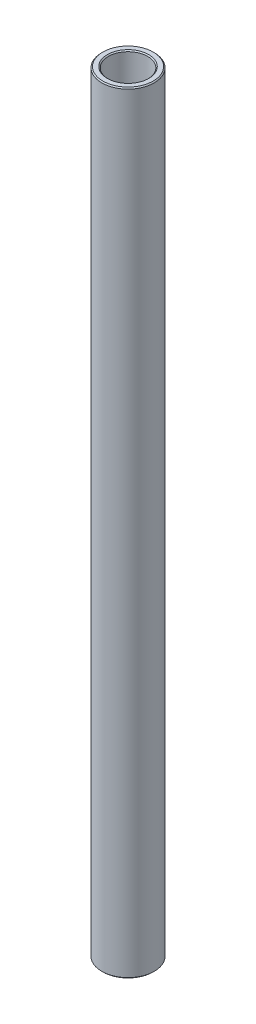
SolidWorks part; units mm, degrees
ref_plane "Front Plane" through (0, 0, 0) normal (0, 0, 1) x (1, 0, 0)
ref_plane "Top Plane" through (0, 0, 0) normal (0, 1, 0) x (1, 0, 0)
ref_plane "Right Plane" through (0, 0, 0) normal (1, 0, 0) x (0, 0, -1)
sketch "Sketch1" plane through (0, 0, 0) normal (0, 0, 1) x (1, 0, 0)
  line L0 (4.7625, 126.3646) -> (4.7625, 313.2672)
  line L1 (4.7625, 313.2672) -> (6.35, 313.2672)
  line L2 (6.35, 313.2672) -> (6.35, 126.3646)
  line L3 (6.35, 126.3646) -> (4.7625, 126.3646)
  line L4 (-10.0875, 135.0958) -> (-120.0875, 135.0958) construction
  line L6 (0, 116.8396) -> (0, 322.7922) construction
  dimension "D1" = 9.525
  dimension "D2" = 9.525
  dimension "D3" = 12.7
  dimension "D4" = 9.525
revolve "Revolve1" add sketch "Sketch1" angle 360 about L6
chamfer "Chamfer1" distance 0.254 angle 45 4 edges at (6.35, 313.2672, 0) (4.7625, 313.2672, 0) (4.7625, 126.3646, 0) (6.35, 126.3646, 0)
equation "\"D4@Sketch1\"=\"D1@Sketch1\""
